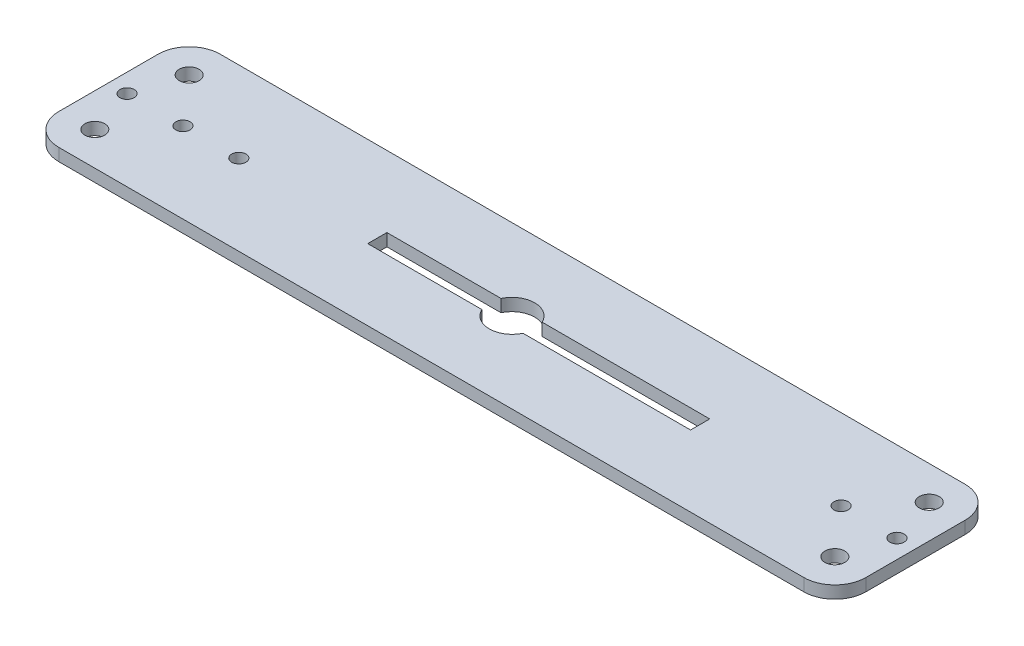
SolidWorks part; units mm, degrees
material "Fibra de Vidro S"
ref_plane "Plano frontal" through (0, 0, 0) normal (0, 0, 1) x (1, 0, 0)
ref_plane "Plano superior" through (0, 0, 0) normal (0, 1, 0) x (1, 0, 0)
ref_plane "Plano direito" through (0, 0, 0) normal (1, 0, 0) x (0, 0, -1)
sketch "Esboço1" plane through (0, 0, 0) normal (0, 1, 0) x (1, 0, 0)
  line L0 (3.3071, -1.5444) -> (30.3071, -1.5444)
  line L1 (-60, -13) -> (60, -13)
  line L2 (-65, -8) -> (-65, 8)
  line L3 (-60, 13) -> (60, 13)
  line L4 (65, -8) -> (65, 8)
  line L5 (-65, -13) -> (-62.2714, -12.4543) construction
  line L6 (-65, 13) -> (-62.2714, 12.4543) construction
  line L7 (-21.6929, 1.5444) -> (-3.3071, 1.5444)
  line L8 (-21.6929, 1.5444) -> (-21.6929, -1.5444)
  line L9 (-21.6929, -1.5444) -> (-3.3071, -1.5444)
  line L10 (30.3071, 1.5444) -> (30.3071, -1.5444)
  line L13 (62.2714, -12.4543) -> (65, -13) construction
  line L16 (62.2714, 12.4543) -> (65, 13) construction
  line L17 (3.3071, 1.5444) -> (30.3071, 1.5444)
  arc A0 (65, 8) -> (60, 13) centre (60, 8) ccw
  arc A1 (65, -8) -> (60, -13) centre (60, -8) cw
  arc A2 (-60, -13) -> (-65, -8) centre (-60, -8) cw
  arc A3 (-65, 8) -> (-60, 13) centre (-60, 8) cw
  arc A4 (-3.3071, -1.5444) -> (3.3071, -1.5444) centre (0, 0) ccw
  arc A5 (3.3071, 1.5444) -> (-3.3071, 1.5444) centre (0, 0) ccw
  circle A6 centre (59.6, 7.6) radius 1.6
  circle A7 centre (59.6, -7.6) radius 1.6
  circle A8 centre (62, 0) radius 1.15
  circle A9 centre (53, 0) radius 1.15
  circle A10 centre (-59.6, 7.6) radius 1.6
  circle A11 centre (-59.6, -7.6) radius 1.6
  circle A12 centre (-53, 0) radius 1.15
  circle A13 centre (-62, 0) radius 1.15
  circle A14 centre (-57.2, 0) radius 1.15 [skipped]
  circle A15 centre (-44, 0) radius 1.15
  point P0 (0, 0)
  dimension "D3" = 5
  dimension "D4" = 7.3
  dimension "D7" = 5.4
  dimension "D9" = 3.2
  dimension "D11" = 2.3
  dimension "D15" = 5.4
  dimension "D16" = 3
  dimension "D17" = 2.3
  dimension "D19" = 9
  dimension "D1" = 130
  dimension "D2" = 26
  dimension "D5" = 52
  dimension "D6" = 27
  dimension "D8" = 5.4
  dimension "D10" = 5.4
  dimension "D12" = 9
  dimension "D13" = 3
  dimension "D18" = 9
  dimension "D14" = 2
extrude "Ressalto-extrusão1" add sketch "Esboço1" along normal blind 2
